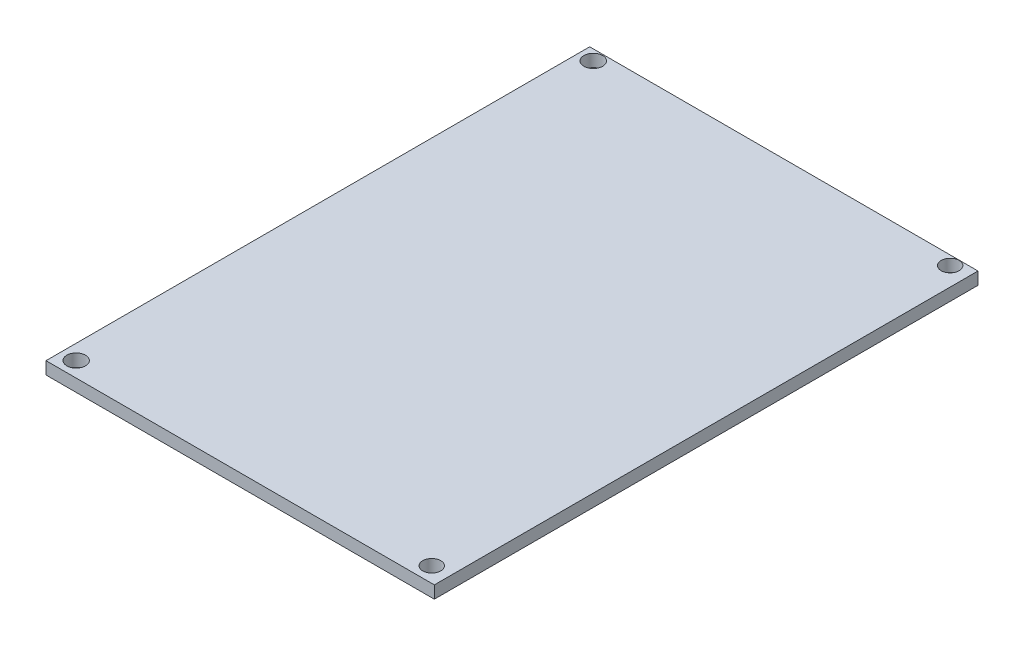
SolidWorks part; units mm, degrees
ref_plane "Płaszczyzna przednia" through (0, 0, 0) normal (0, 0, 1) x (1, 0, 0)
ref_plane "Płaszczyzna górna" through (0, 0, 0) normal (0, 1, 0) x (1, 0, 0)
ref_plane "Płaszczyzna prawa" through (0, 0, 0) normal (1, 0, 0) x (0, 0, -1)
sketch "Sketch1" plane through (0, 0, 0) normal (0, 1, 0) x (1, 0, 0)
  line L1 (-30, -49.8246) -> (20, -49.8246)
  line L2 (-30, -49.8246) -> (-30, 20.1754)
  line L3 (-30, 20.1754) -> (20, 20.1754)
  line L4 (20, -49.8246) -> (20, 20.1754)
  dimension "D1" = 50
  dimension "D2" = 70
extrude "Boss-Extrude1" add sketch "Sketch1" along normal blind 1.6
sketch "Sketch2" plane through (0, 1.6, 0) normal (0, 1, 0) x (1, 0, 0)
  circle A0 centre (-28.1905, 18.8326) radius 1.2067
  circle A1 centre (17.6043, 18.9877) radius 1.1543
  circle A2 centre (17.7056, -47.8642) radius 1.1549
  circle A3 centre (-28.0742, -47.8642) radius 1.2004
extrude "Cut-Extrude1" cut sketch "Sketch2" against normal blind 10
